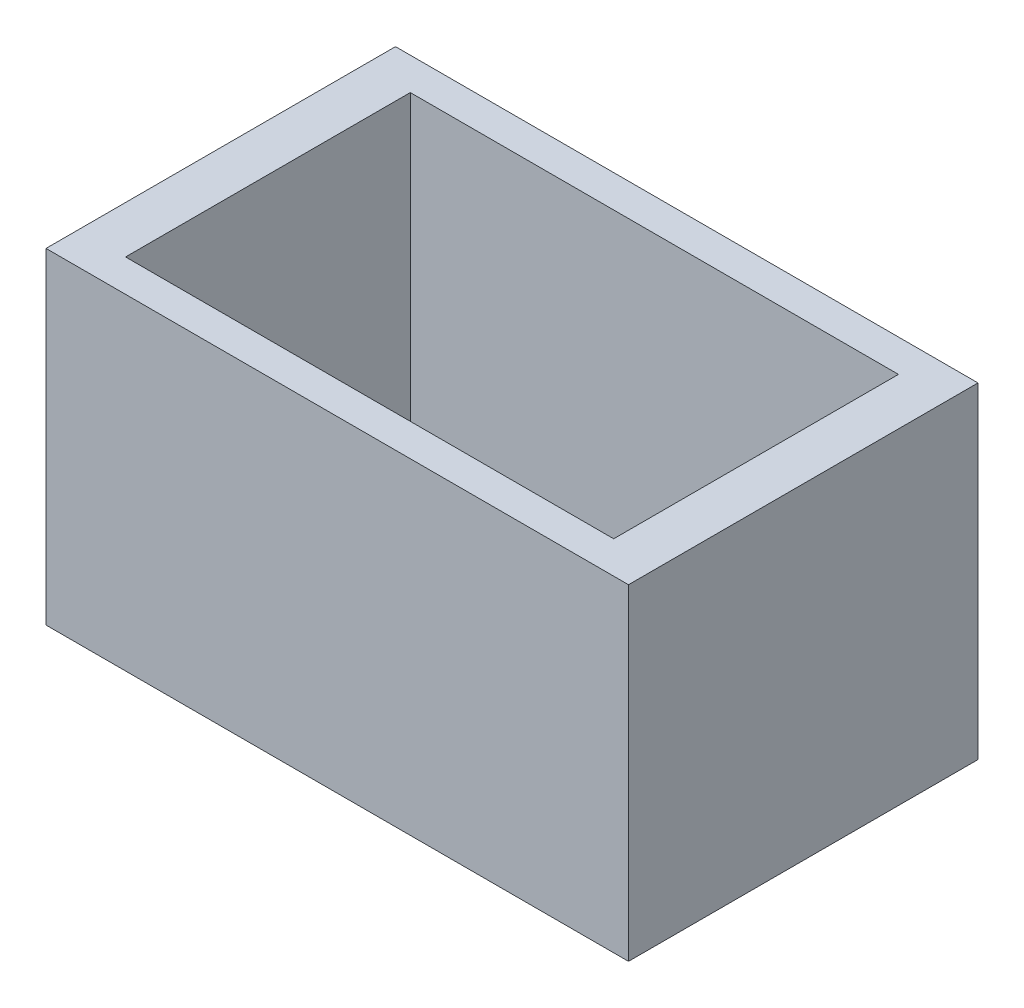
SolidWorks part; units mm, degrees
ref_plane "Front Plane" through (0, 0, 0) normal (0, 0, 1) x (1, 0, 0)
ref_plane "Top Plane" through (0, 0, 0) normal (0, 1, 0) x (1, 0, 0)
ref_plane "Right Plane" through (0, 0, 0) normal (1, 0, 0) x (0, 0, -1)
sketch "Sketch1" plane through (0, 0, 0) normal (0, 1, 0) x (1, 0, 0)
  line L1 (125, 75) -> (-125, 75)
  line L2 (125, 75) -> (125, -75)
  line L3 (125, -75) -> (-125, -75)
  line L4 (-125, 75) -> (-125, -75)
  line L5 (125, 75) -> (-125, -75) construction
  line L6 (125, -75) -> (-125, 75) construction
  point P0 (0, 0)
  dimension "D1" = 250
  dimension "D2" = 150
extrude "Boss-Extrude1" add sketch "Sketch1" along normal blind 140
ref_plane "Plane1" through (0, 140, 0) normal (0, 1, 0) x (1, 0, 0)
sketch "Sketch2" plane through (0, 140, 0) normal (0, 1, 0) x (1, 0, 0)
  line L1 (104.7525, 61.1056) -> (-104.7525, 61.1056)
  line L2 (104.7525, 61.1056) -> (104.7525, -61.1056)
  line L3 (104.7525, -61.1056) -> (-104.7525, -61.1056)
  line L4 (-104.7525, 61.1056) -> (-104.7525, -61.1056)
  line L5 (104.7525, 61.1056) -> (-104.7525, -61.1056) construction
  line L6 (104.7525, -61.1056) -> (-104.7525, 61.1056) construction
  point P0 (0, 0)
extrude "Cut-Extrude1" cut sketch "Sketch2" against normal blind 130
